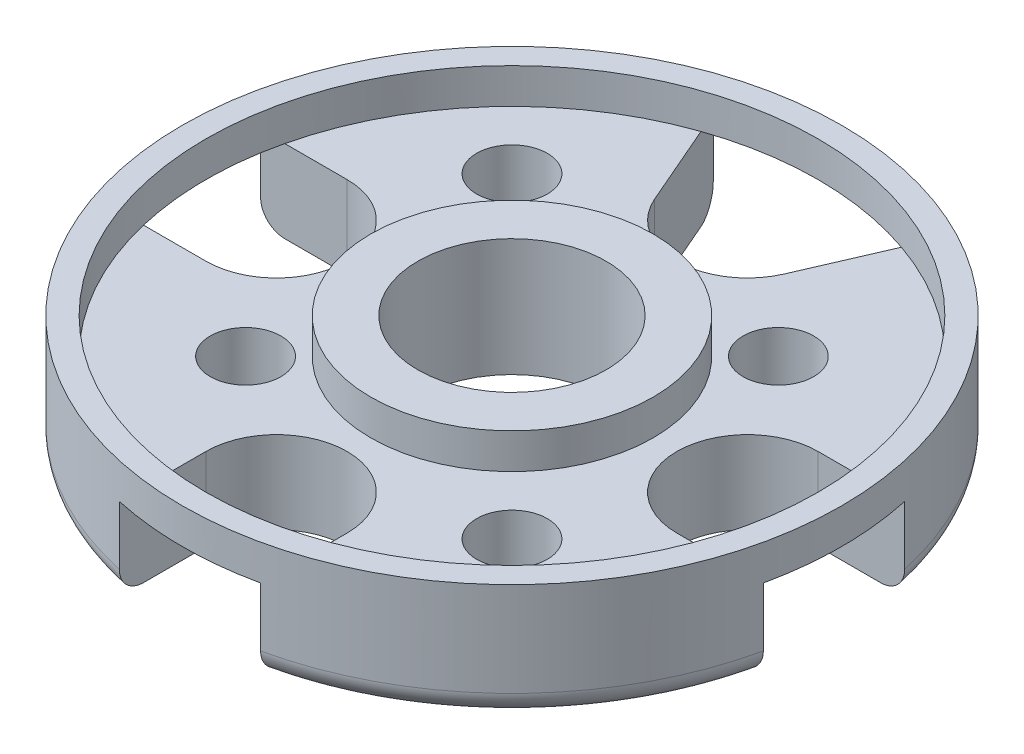
SolidWorks part; units mm, degrees
ref_plane "XY" through (0, 0, 0) normal (0, 0, 1) x (1, 0, 0)
ref_plane "XZ" through (0, 0, 0) normal (0, 1, 0) x (1, 0, 0)
ref_plane "YZ" through (0, 0, 0) normal (1, 0, 0) x (0, 0, -1)
sketch "Esquisse1" plane through (0, 0, 0) normal (0, 1, 0) x (1, 0, 0)
  circle A0 centre (0, 0) radius 14
  dimension "D1" = 28
extrude "base brut" add sketch "Esquisse1" along normal blind 5
fillet "Congé1" radius 1 1 edges at (0, 0, 14)
sketch "Esquisse2" plane through (0, 5, 0) normal (0, 1, 0) x (1, 0, 0)
  circle A3 centre (0, 0) radius 13
  circle A4 centre (0, 0) radius 13
  dimension "D1" = 1
extrude "creux interieur" cut sketch "Esquisse2" against normal blind 1.5
sketch "Esquisse3" plane through (0, 0, 0) normal (0, -1, 0) x (1, 0, 0)
  line L0 (0, 15.0918) -> (0, -15.6528) construction
  line L1 (16.4944, 0) -> (-15.7463, 0) construction
  line L2 (10, 3) -> (14, -3) construction
  line L3 (10, 3) -> (14, 3)
  line L5 (10, -3) -> (14, -3)
  line L6 (14, 3) -> (14, -3)
  circle A0 centre (0, 0) radius 14 construction
  arc A1 (10, 3) -> (10, -3) centre (10, 0) ccw
  point P9 (12, 0)
  dimension "D3" = 3
  dimension "D1" = 4
  dimension "D2" = 6
extrude "creusement exterieur" cut sketch "Esquisse3" against normal up to surface (3.5 mm away) up to face at (0, 3.5, 13)
pattern_circular "Répétition circulaire1" count 3 every 90 about axis through (0, 0, 0) along (0, 1, 0) of "creusement exterieur"
sketch "Esquisse4" plane through (0, 0, 0) normal (0, -1, 0) x (1, 0, 0)
  line L0 (0, 15.765) -> (0, -14.9048) construction
  line L1 (-5, -14) -> (5, -14)
  line L2 (-5, -14) -> (-2.7532, -8.8085)
  line L3 (5, -14) -> (2.7532, -8.8085)
  circle A0 centre (0, 0) radius 10 construction
  arc A1 (-13.6748, -3) -> (13.6748, -3) centre (0, 0) ccw construction
  arc A2 (-2.7532, -8.8085) -> (2.7532, -8.8085) centre (0, -10) cw
  point P11 (0, -14)
  dimension "D2" = 3
  dimension "D1" = 10
extrude "passage fils" cut sketch "Esquisse4" against normal up to surface (3.5 mm away) up to face at (0, 3.5, 2.9195)
sketch "Esquisse5" plane through (0, 3.5, 0) normal (0, 1, 0) x (-1, 0, 0)
  circle A0 centre (0, 0) radius 4
  dimension "D1" = 8
extrude "passage axe rotor" cut sketch "Esquisse5" against normal through all
sketch "Esquisse6" plane through (0, 3.5, 0) normal (0, 1, 0) x (1, 0, 0)
  circle A0 centre (0, 0) radius 4 construction
  circle A1 centre (0, 0) radius 4
  circle A2 centre (0, 0) radius 6
  dimension "D1" = 2
extrude "bossage axe rotor" add sketch "Esquisse6" along normal up to surface (1.5 mm away) up to face at (0, 5, 13)
sketch "Esquisse7" plane through (0, 0, 0) normal (0, -1, 0) x (1, 0, 0)
  line L0 (0, 14.5682) -> (0, 0) construction
  line L1 (-11.7366, 11.7366) -> (11.7366, -11.7366) construction
  line L2 (11.7366, 11.7366) -> (-11.7366, -11.7366) construction
  circle A0 centre (-5.6569, 5.6569) radius 1.5
  circle A1 centre (5.6569, -5.6569) radius 1.5
  circle A2 centre (6.7175, 6.7175) radius 1.5
  circle A3 centre (-6.7175, -6.7175) radius 1.5
  dimension "D5" = 3
  dimension "D6" = 3
  dimension "D7" = 19
  dimension "D9" = 3
  dimension "D1" = 45
  dimension "D2" = 45
  dimension "D3" = 16
  dimension "D4" = 8
  dimension "D8" = 9.5
extrude "M3" cut sketch "Esquisse7" against normal through all
